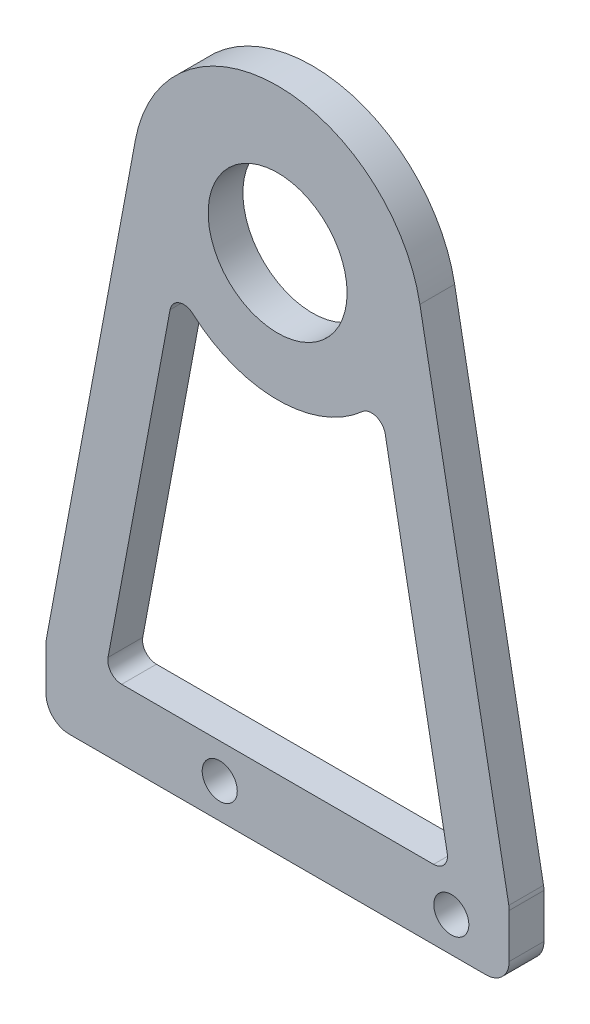
SolidWorks part; units mm, degrees
material "Thornel Mat VMA"
ref_plane "前视基准面" through (0, 0, 0) normal (0, 0, 1) x (1, 0, 0)
ref_plane "上视基准面" through (0, 0, 0) normal (0, 1, 0) x (1, 0, 0)
ref_plane "右视基准面" through (0, 0, 0) normal (1, 0, 0) x (0, 0, -1)
sketch "草图1" plane through (0, 0, 0) normal (0, 0, 1) x (1, 0, 0)
  line L0 (0, 0) -> (0, -45) construction
  line L1 (-20, -45) -> (20, -45)
  line L2 (20, -45) -> (20, -39)
  line L3 (20, -39) -> (12.2875, 2.2949)
  line L4 (-20, -39) -> (-12.2875, 2.2949)
  line L5 (-20, -45) -> (-20, -39)
  circle A0 centre (0, 0) radius 6
  arc A1 (12.2875, 2.2949) -> (-12.2875, 2.2949) centre (0, 0) ccw
  point P8 (0, -45)
  dimension "D1" = 12
  dimension "D2" = 25
  dimension "D3" = 45
  dimension "D4" = 40
  dimension "D5" = 6
extrude "凸台-拉伸1" add sketch "草图1" along normal blind 3
fillet "圆角1" radius 2 4 edges at (-20, -45, 1.5) (-20, -39, 1.5) (20, -39, 1.5) (20, -45, 1.5)
sketch "草图2" plane through (0, 0, 3) normal (0, 0, 1) x (1, 0, 0)
  circle A0 centre (15, -42) radius 1.25 construction
  circle A1 centre (-5, -42) radius 1.25 construction
  circle A2 centre (15, -42) radius 1.25 construction
  circle A3 centre (-5, -42) radius 1.25 construction
  circle A4 centre (-5, -42) radius 1.515
  circle A5 centre (15, -42) radius 1.515
  dimension "D1" = 3.03
extrude "切除-拉伸1" cut sketch "草图2" against normal blind 10
sketch "草图3" plane through (0, 0, 3) normal (0, 0, 1) x (1, 0, 0)
  line L0 (-8.8498, -6.533) -> (-14.9135, -39)
  line L1 (-14.9135, -39) -> (14.9135, -39)
  line L2 (14.9135, -39) -> (8.8498, -6.533)
  line L3 (19.966, -38.818) -> (12.2875, 2.2949) construction
  line L4 (-12.2875, 2.2949) -> (-19.966, -38.818) construction
  arc A0 (-8.8498, -6.533) -> (8.8498, -6.533) centre (0, 0) ccw
  circle A1 centre (0, 0) radius 6 construction
  circle A2 centre (-5, -42) radius 1.515 construction
  dimension "D1" = 5
  dimension "D2" = 3
  dimension "D3" = 5
  dimension "D4" = 5
extrude "切除-拉伸2" cut sketch "草图3" against normal blind 10
fillet "圆角2" radius 1.2 4 edges at (14.9135, -39, 1.5) (8.8498, -6.533, 1.5) (-14.9135, -39, 1.5) (-8.8498, -6.533, 1.5)
